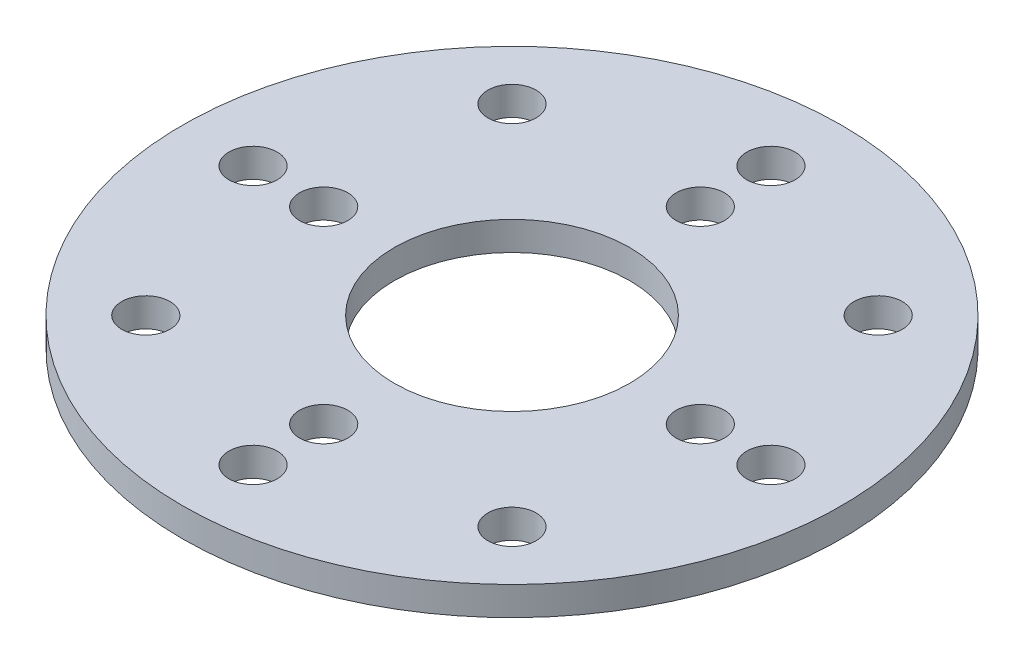
SolidWorks part; units mm, degrees
ref_plane "Front Plane" through (0, 0, 0) normal (0, 0, 1) x (1, 0, 0)
ref_plane "Top Plane" through (0, 0, 0) normal (0, 1, 0) x (1, 0, 0)
ref_plane "Right Plane" through (0, 0, 0) normal (1, 0, 0) x (0, 0, -1)
ref_plane "Plane1" through (0, 1.72, 0) normal (0, 1, 0) x (1, 0, 0)
sketch "Sketch1" plane through (0, 1.72, 0) normal (0, 1, 0) x (1, 0, 0)
  circle A0 centre (-8, 0) radius 1.025
  circle A1 centre (8, 0) radius 1.025
  circle A2 centre (-7.7782, 7.7782) radius 1.025
  circle A3 centre (-7.7782, -7.7782) radius 1.025
  circle A4 centre (7.7782, -7.7782) radius 1.025
  circle A5 centre (7.7782, 7.7782) radius 1.025
  circle A6 centre (0, 11) radius 1.025
  circle A7 centre (11, 0) radius 1.025
  circle A8 centre (0, -11) radius 1.025
  circle A9 centre (-11, 0) radius 1.025
  circle A10 centre (0, 8) radius 1.025
  circle A11 centre (0, -8) radius 1.025
  circle A12 centre (0, 0) radius 14
  circle A13 centre (0, 0) radius 5
extrude "Boss-Extrude1" add sketch "Sketch1" against normal blind 1.22
